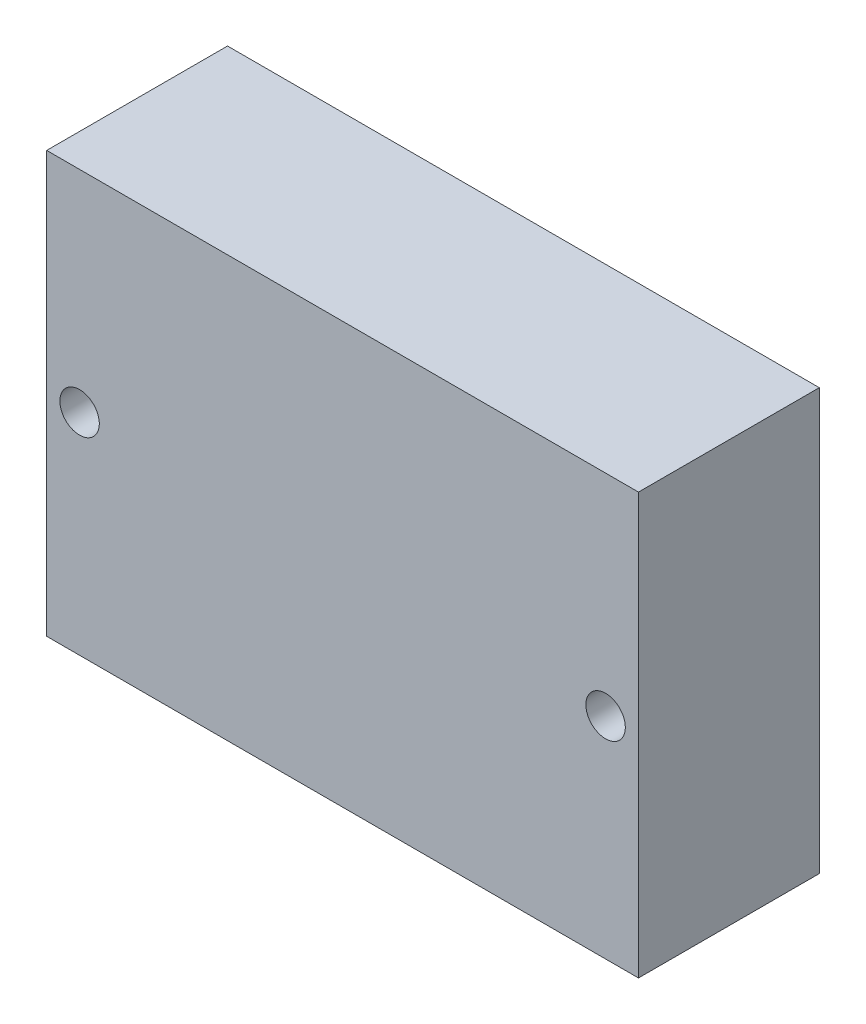
SolidWorks part; units mm, degrees
ref_plane "Front Plane" through (0, 0, 0) normal (0, 0, 1) x (1, 0, 0)
ref_plane "Top Plane" through (0, 0, 0) normal (0, 1, 0) x (1, 0, 0)
ref_plane "Right Plane" through (0, 0, 0) normal (1, 0, 0) x (0, 0, -1)
sketch "Sketch1" plane through (0, 0, 0) normal (0, 0, 1) x (1, 0, 0)
  line L0 (34.65, -24.64) -> (68.0188, -24.64) construction
  line L1 (12.15, -8.64) -> (57.15, -8.64)
  line L2 (12.15, -8.64) -> (12.15, -40.64)
  line L3 (12.15, -40.64) -> (57.15, -40.64)
  line L4 (57.15, -8.64) -> (57.15, -40.64)
  line L5 (12.15, -8.64) -> (57.15, -40.64) construction
  line L6 (12.15, -40.64) -> (57.15, -8.64) construction
  line L7 (68.0188, -24.64) -> (7.5994, -24.64) construction
  line L8 (34.65, -24.64) -> (34.65, -6.5359) construction
  circle A0 centre (54.65, -24.64) radius 1.5
  circle A2 centre (14.65, -24.64) radius 1.5
  point P0 (34.65, -24.64)
  dimension "D3" = 3
  dimension "D1" = 45
  dimension "D2" = 32
  dimension "D4" = 20
extrude "Boss-Extrude1" add sketch "Sketch1" along normal blind 13.75
